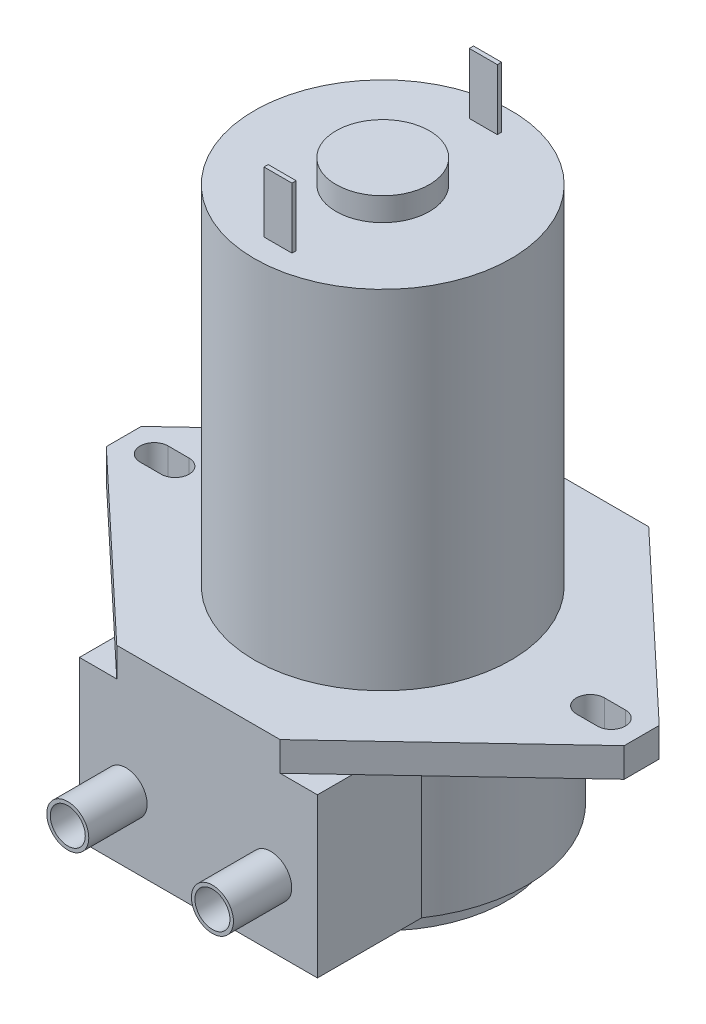
SolidWorks part; units mm, degrees
ref_plane "Front Plane" through (0, 0, 0) normal (0, 0, 1) x (1, 0, 0)
ref_plane "Top Plane" through (0, 0, 0) normal (0, 1, 0) x (1, 0, 0)
ref_plane "Right Plane" through (0, 0, 0) normal (1, 0, 0) x (0, 0, -1)
sketch "Sketch1" plane through (0, 0, 0) normal (0, 1, 0) x (1, 0, 0)
  line L1 (-17.2687, 17.2846) -> (0.5113, 17.2846)
  line L2 (-36.5727, -0.8764) -> (-36.5727, -4.6864)
  line L3 (-17.2687, -22.8474) -> (0.5113, -22.8474)
  line L4 (19.8153, -0.8764) -> (19.8153, -4.6864)
  line L9 (-36.5727, -0.8764) -> (-17.2687, 17.2846)
  line L10 (19.8153, -0.8764) -> (0.5113, 17.2846)
  line L11 (19.8153, -4.6864) -> (0.5113, -22.8474)
  line L12 (-17.2687, -22.8474) -> (-36.5727, -4.6864)
extrude "Boss-Extrude1" add sketch "Sketch1" along normal blind 3.175
sketch "Sketch2" plane through (0, 3.175, 0) normal (0, 1, 0) x (1, 0, 0)
  line L0 (19.8153, -2.7814) -> (-36.5727, -2.7814) construction
  line L1 (19.8153, -4.6864) -> (19.8153, -0.8764) construction
  line L2 (-36.5727, -0.8764) -> (-36.5727, -4.6864) construction
  line L3 (0.5113, 17.2846) -> (-17.2687, 17.2846) construction
  line L4 (-17.2687, -22.8474) -> (0.5113, -22.8474) construction
  line L5 (-8.3787, 17.2846) -> (-8.3787, -22.8474) construction
  circle A0 centre (-8.3787, -2.7814) radius 13.97
  dimension "D1" = 27.94
extrude "Boss-Extrude2" add sketch "Sketch2" along normal blind 37.846
sketch "Sketch3" plane through (0, 41.021, 0) normal (0, 1, 0) x (1, 0, 0)
  circle A0 centre (-8.3787, -2.7814) radius 5.08
  dimension "D1" = 10.16
extrude "Boss-Extrude3" add sketch "Sketch3" along normal blind 2.54
sketch "Sketch5" plane through (0, 41.021, 0) normal (0, 1, 0) x (1, 0, 0)
  line L0 (-8.3787, -2.7814) -> (5.5913, -2.7814) construction
  line L1 (5.5913, -2.7814) -> (-22.3487, -2.7814) construction
  line L2 (-8.3787, -2.7814) -> (-8.3787, -22.8474) construction
  line L3 (-17.2687, -22.8474) -> (0.5113, -22.8474) construction
  line L4 (-8.3787, -2.7814) -> (-8.3787, 17.2846) construction
  line L5 (0.5113, 17.2846) -> (-17.2687, 17.2846) construction
  line L6 (9.9608, 8.3946) -> (-26.7182, 8.3946) construction
  line L7 (19.8153, -0.8764) -> (0.5113, 17.2846) construction
  line L8 (-17.2687, 17.2846) -> (-36.5727, -0.8764) construction
  line L9 (9.9608, -13.9574) -> (-26.7182, -13.9574) construction
  line L10 (0.5113, -22.8474) -> (19.8153, -4.6864) construction
  line L11 (-36.5727, -4.6864) -> (-17.2687, -22.8474) construction
  line L13 (-9.9027, 8.6232) -> (-6.8547, 8.6232)
  line L14 (-9.9027, 8.6232) -> (-9.9027, 8.166)
  line L15 (-9.9027, 8.166) -> (-6.8547, 8.166)
  line L16 (-6.8547, 8.6232) -> (-6.8547, 8.166)
  line L17 (-9.9027, 8.6232) -> (-6.8547, 8.166) construction
  line L18 (-9.9027, 8.166) -> (-6.8547, 8.6232) construction
  line L19 (-9.9027, -14.186) -> (-6.8547, -14.186)
  line L20 (-9.9027, -14.186) -> (-9.9027, -13.7288)
  line L21 (-9.9027, -13.7288) -> (-6.8547, -13.7288)
  line L22 (-6.8547, -14.186) -> (-6.8547, -13.7288)
  line L23 (-9.9027, -14.186) -> (-6.8547, -13.7288) construction
  line L24 (-9.9027, -13.7288) -> (-6.8547, -14.186) construction
  circle A0 centre (-8.3787, -2.7814) radius 13.97 construction
  circle A1 centre (-8.3787, -2.7814) radius 13.97 construction
  point P27 (-8.3787, 8.3946)
  point P32 (-8.3787, -13.9574)
  dimension "D1" = 11.176
  dimension "D2" = 11.176
  dimension "D3" = 3.048
  dimension "D4" = 0.4572
  dimension "D5" = 0.4572
  dimension "D6" = 3.048
extrude "Boss-Extrude4" add sketch "Sketch5" along normal blind 6.604 separate body
sketch "Sketch6" plane through (0, 0, 0) normal (0, -1, 0) x (1, 0, 0)
  line L0 (-21.3327, 11.5112) -> (-21.3327, 22.8474) construction
  line L1 (4.5753, 11.5112) -> (4.5753, 22.8474) construction
  line L2 (-21.1, 22.8474) -> (4.5753, 22.8474)
  line L3 (-21.3327, 22.8474) -> (-21.3327, 11.5112)
  line L5 (4.5753, 22.8474) -> (4.5753, 11.5112)
  line L6 (-21.1, 22.8474) -> (-21.3327, 22.8474)
  arc A0 (-21.3327, 11.5112) -> (4.5753, 11.5112) centre (-8.3787, 2.7814) ccw
  dimension "D1" = 31.242
extrude "Boss-Extrude5" add sketch "Sketch6" along normal blind 17.272
sketch "Sketch7" plane through (0, -17.272, 0) normal (0, -1, 0) x (1, 0, 0)
  circle A0 centre (-8.3787, 2.7814) radius 13.462
  dimension "D1" = 26.924
extrude "Boss-Extrude6" add sketch "Sketch7" along normal blind 2.54
sketch "Sketch8" plane through (0, 0, 22.8474) normal (0, 0, 1) x (1, 0, 0)
  circle A0 centre (-0.5047, -10.16) radius 2.286
  circle A1 centre (-16.2527, -10.16) radius 2.286
  dimension "D4" = 4.572
  dimension "D5" = 4.572
extrude "Boss-Extrude7" add sketch "Sketch8" along normal blind 6.35
sketch "Sketch9" plane through (0, 0, 29.1974) normal (0, 0, 1) x (1, 0, 0)
  circle A0 centre (-0.5047, -10.16) radius 1.905
  circle A1 centre (-16.2527, -10.16) radius 1.905
  dimension "D1" = 3.81
  dimension "D2" = 3.81
extrude "Cut-Extrude1" cut sketch "Sketch9" against normal blind 6.35
sketch "Sketch10" plane through (0, 0, 0) normal (0, -1, 0) x (1, 0, 0)
  line L0 (16.5133, -2.2301) -> (16.5133, 1.2574) construction
  line L1 (19.8153, 0.8764) -> (0.5113, -17.2846) construction
  line L2 (4.5753, 19.0241) -> (19.8153, 4.6864) construction
  line L3 (-33.2707, -2.2301) -> (-33.2707, 1.2574) construction
  line L4 (-17.2687, -17.2846) -> (-36.5727, 0.8764) construction
  line L5 (-36.5727, 4.6864) -> (-21.3327, 19.0241) construction
  line L6 (19.8153, 4.6864) -> (19.8153, 0.8764) construction
  line L7 (-36.5727, 0.8764) -> (-36.5727, 4.6864) construction
  line L8 (14.2273, -4.3807) -> (14.2273, 1.2574) construction
  line L9 (-30.9847, -4.3807) -> (-30.9847, 1.2574) construction
  line L10 (16.5133, 4.3054) -> (14.2273, 1.2574) construction
  line L11 (14.2273, 4.3054) -> (16.5133, 1.2574) construction
  line L12 (-30.9847, 1.2574) -> (-33.2707, 4.3054) construction
  line L13 (16.5133, 1.2574) -> (14.2273, 1.2574)
  line L14 (16.5133, 4.3054) -> (14.2273, 4.3054)
  line L16 (16.5133, 2.7814) -> (16.5133, 7.7929) construction
  line L18 (-33.2707, 1.2574) -> (-30.9847, 1.2574)
  line L19 (-33.2707, 4.3054) -> (-30.9847, 4.3054)
  line L20 (-33.2707, 4.3054) -> (-33.2707, 7.7929) construction
  line L21 (-30.9847, 4.3054) -> (-30.9847, 9.9436) construction
  arc A0 (16.5133, 1.2574) -> (16.5133, 4.3054) centre (16.5133, 2.7814) ccw
  arc A1 (14.2273, 4.3054) -> (14.2273, 1.2574) centre (14.2273, 2.7814) ccw
  arc A2 (-30.9847, 1.2574) -> (-30.9847, 4.3054) centre (-30.9847, 2.7814) ccw
  circle A3 centre (15.3703, 2.7814) radius 1.143 construction
  circle A4 centre (-32.1277, 2.7814) radius 1.0104 construction
  arc A5 (-33.2707, 4.3054) -> (-33.2707, 1.2574) centre (-33.2707, 2.7814) ccw
  dimension "D1" = 3.302
  dimension "D2" = 3.302
  dimension "D3" = 2.286
  dimension "D4" = 2.286
extrude "Cut-Extrude2" cut sketch "Sketch10" against normal up to next (3.175 mm away)
